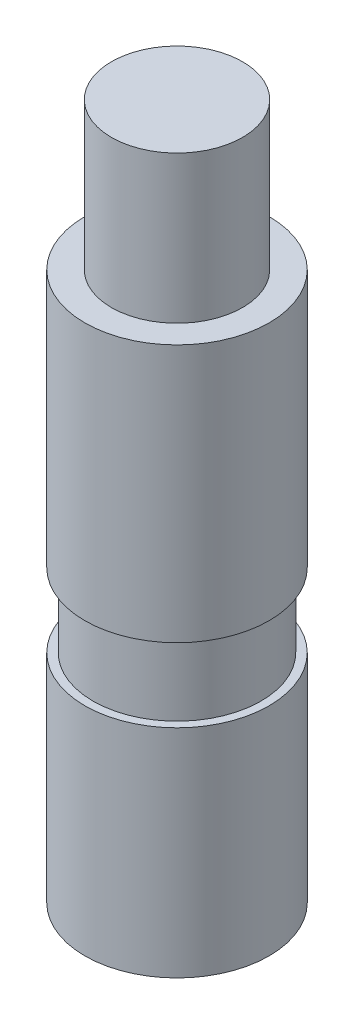
SolidWorks part; units mm, degrees
material "Reg 2 mat'l"
ref_plane "Front Plane" through (0, 0, 0) normal (0, 0, 1) x (1, 0, 0)
ref_plane "Top Plane" through (0, 0, 0) normal (0, 1, 0) x (1, 0, 0)
ref_plane "Right Plane" through (0, 0, 0) normal (1, 0, 0) x (0, 0, -1)
sketch "Sketch1" plane through (0, 0, 0) normal (0, 1, 0) x (1, 0, 0)
  circle A0 centre (0, 0) radius 15.875
  dimension "D1" = 31.75
extrude "Boss-Extrude1" add sketch "Sketch1" along normal blind 119.888
sketch "Sketch2" plane through (0, 119.888, 0) normal (0, 1, 0) x (1, 0, 0)
  circle A0 centre (0, 0) radius 15.875
  circle A1 centre (0, 0) radius 11.303
  dimension "D1" = 22.606
extrude "Cut-Extrude1" cut sketch "Sketch2" against normal blind 25.4
sketch "Sketch3" plane through (0, 119.888, 0) normal (0, 1, 0) x (1, 0, 0)
  circle A0 centre (0, 0) radius 15.875
  circle A1 centre (0, 0) radius 14.478
  dimension "D1" = 28.956
extrude "Cut-Extrude2" cut sketch "Sketch3" against normal blind 12.7 from offset 69.85 offset against normal yes
